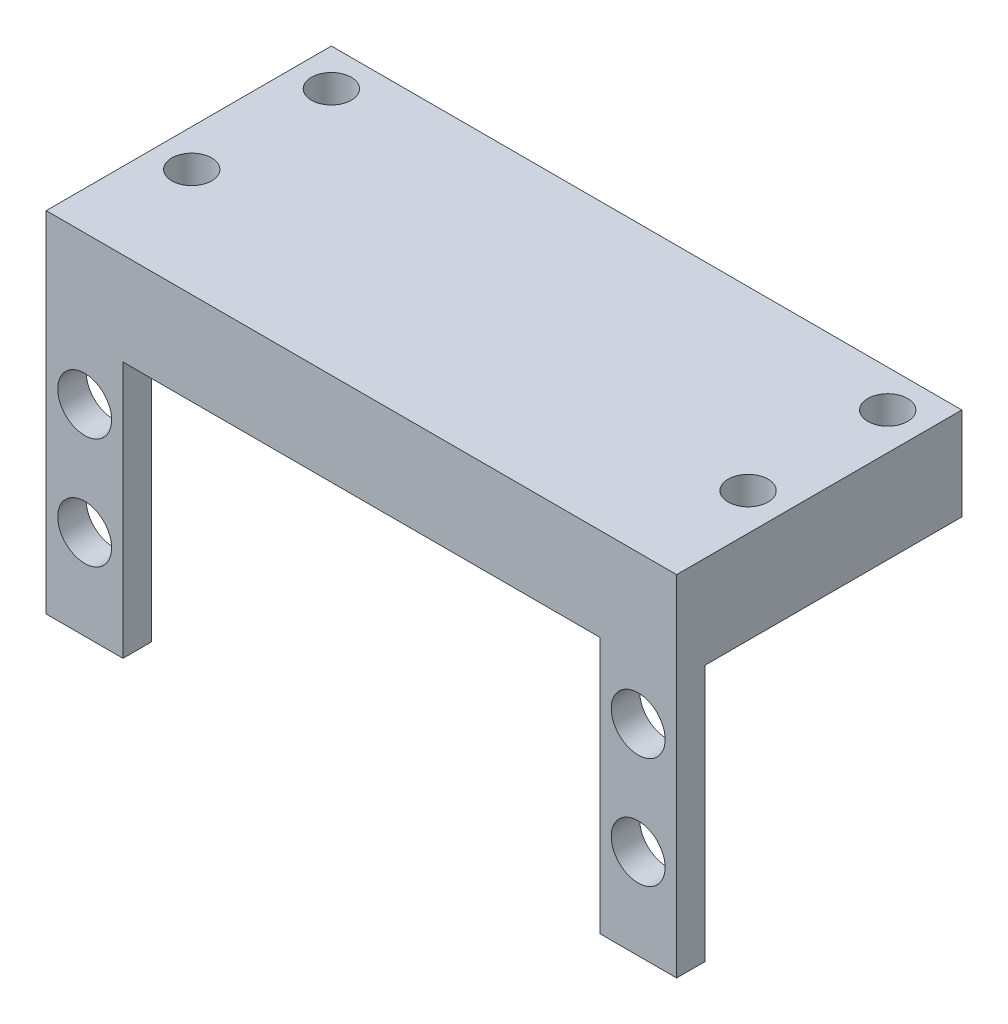
SolidWorks part; units mm, degrees
ref_plane "Front Plane" through (0, 0, 0) normal (0, 0, 1) x (1, 0, 0)
ref_plane "Top Plane" through (0, 0, 0) normal (0, 1, 0) x (1, 0, 0)
ref_plane "Right Plane" through (0, 0, 0) normal (1, 0, 0) x (0, 0, -1)
sketch "Sketch1" plane through (0, 0, 0) normal (0, 1, 0) x (1, 0, 0)
  line L1 (0, 0) -> (56.15, 0)
  line L2 (0, 0) -> (0, 25.4)
  line L3 (0, 25.4) -> (56.15, 25.4)
  line L4 (56.15, 0) -> (56.15, 25.4)
  dimension "D1" = 56.15
  dimension "D2" = 25.4
extrude "Boss-Extrude1" add sketch "Sketch1" against normal blind 2.54
sketch "Sketch2" plane through (0, 0, 0) normal (0, 0, 1) x (1, 0, 0)
  line L1 (0, 0) -> (56.15, 0)
  line L2 (0, 0) -> (0, -25.4)
  line L3 (0, -25.4) -> (56.15, -25.4)
  line L4 (56.15, 0) -> (56.15, -25.4)
  dimension "D1" = 25.4
extrude "Boss-Extrude2" add sketch "Sketch2" against normal blind 2.54
sketch "Sketch3" plane through (0, 0, 0) normal (0, 0, 1) x (1, 0, 0)
  circle A0 centre (3.425, -7.515) radius 2.4
  circle A1 centre (3.425, -17.385) radius 2.4
  circle A2 centre (52.725, -7.515) radius 2.4
  circle A3 centre (52.725, -17.385) radius 2.4
  dimension "D1" = 4.8
  dimension "D2" = 4.8
  dimension "D3" = 4.8
  dimension "D4" = 4.8
extrude "Cut-Extrude1" cut sketch "Sketch3" against normal through all
sketch "Sketch4" plane through (0, 0, 0) normal (0, 0, 1) x (1, 0, 0)
  line L0 (5.825, -7.515) -> (56.15, -7.515)
  line L1 (56.15, -25.4) -> (56.15, 0) construction
  line L2 (1.025, -7.515) -> (-49.3, -7.515)
  line L3 (-49.3, -25.4) -> (-49.3, -2.54)
  line L5 (0, -25.4) -> (56.15, -25.4) construction
  line L7 (-49.3, 0) -> (-49.3, -2.54) construction
  line L8 (0, 0) -> (56.15, 0) construction
  line L9 (50.325, -7.515) -> (0, -7.515)
  line L10 (0, -25.4) -> (0, 0) construction
  line L11 (55.125, -7.515) -> (105.45, -7.515)
  line L12 (-49.3, -2.54) -> (0, -2.54) construction
  line L13 (105.45, -25.4) -> (105.45, -2.54)
  line L14 (-49.3, -25.4) -> (105.45, -25.4)
  line L15 (105.45, -2.54) -> (-49.3, -2.54)
  circle A0 centre (3.425, -7.515) radius 2.4 construction
  circle A1 centre (52.725, -7.515) radius 2.4 construction
  dimension "D1" = 2.54
ref_plane "Plane3" through (0, -2.54, 0) normal (0, -1, 0) x (-1, 0, 0)
sketch "Sketch11" plane through (0, 0, 0) normal (0, 1, 0) x (1, 0, 0)
  line L1 (56.15, 0) -> (0, 0)
  line L2 (56.15, 0) -> (56.15, 25.4)
  line L3 (56.15, 25.4) -> (0, 25.4)
  line L4 (0, 0) -> (0, 25.4)
extrude "Boss-Extrude3" add sketch "Sketch11" along normal blind 5.715
sketch "Sketch6" plane through (0, -2.54, 0) normal (0, -1, 0) x (1, 0, 0)
  line L0 (51.078, -22.102) -> (54.626, -22.102) construction
  line L5 (51.078, -20.328) -> (54.626, -20.328)
  line L6 (51.078, -20.328) -> (51.078, -23.876)
  line L7 (51.078, -23.876) -> (54.626, -23.876)
  line L8 (54.626, -20.328) -> (54.626, -23.876)
  line L9 (52.852, -22.102) -> (52.852, -23.876) construction
  line L10 (52.852, -22.102) -> (52.852, -20.328) construction
  line L11 (56.15, -25.4) -> (54.626, -25.4)
  line L12 (52.852, -20.328) -> (52.852, -11.438) construction
  line L13 (52.852, -11.438) -> (52.852, -9.664) construction
  line L14 (56.15, -25.4) -> (56.15, -23.876)
  line L15 (56.15, -23.876) -> (54.626, -23.876)
  line L16 (54.626, -25.4) -> (54.626, -23.876)
  line L17 (28.075, -25.4) -> (28.075, -2.54) construction
  line L18 (56.15, -25.4) -> (0, -25.4) construction
  line L19 (56.15, -2.54) -> (0, -2.54) construction
  circle A0 centre (52.852, -22.102) radius 1.774
  circle A2 centre (52.852, -9.664) radius 1.774
  circle A3 centre (3.298, -22.102) radius 1.774
  circle A4 centre (3.298, -9.664) radius 1.774
  dimension "D1" = 8.89
  dimension "D3" = 3.548
  dimension "D4" = 3.548
  dimension "D5" = 1.524
  dimension "D6" = 1.524
extrude "Cut-Extrude3" cut sketch "Sketch6" against normal through all contours A0 | A2 | A4 | A3
sketch "Sketch7" plane through (0, 0, 0) normal (0, 0, 1) x (1, 0, 0)
  line L5 (5.825, -7.515) -> (6.841, -7.515)
  line L6 (5.825, -7.515) -> (56.15, -7.515) construction
  line L7 (6.841, -7.515) -> (6.841, -25.4) construction
  line L8 (-49.3, -25.4) -> (105.45, -25.4) construction
  line L9 (50.325, -17.385) -> (49.309, -17.385) construction
  line L12 (105.45, -2.54) -> (-49.3, -2.54) construction
  line L13 (49.309, -17.385) -> (49.309, -25.4) construction
  line L16 (6.841, -2.54) -> (49.309, -2.54)
  line L17 (6.841, -2.54) -> (6.841, -25.4)
  line L18 (6.841, -25.4) -> (49.309, -25.4)
  line L19 (49.309, -2.54) -> (49.309, -25.4)
  circle A0 centre (52.725, -17.385) radius 2.4 construction
  line M8 (0, -25.4) -> (56.15, -25.4)
  dimension "D1" = 1.016
  dimension "D3" = 1.016
extrude "Cut-Extrude4" cut sketch "Sketch7" against normal through all contours L19 L16 L17 M8
sketch "Sketch8" plane through (0, -2.54, 0) normal (0, -1, 0) x (1, 0, 0)
  line L0 (56.15, -25.4) -> (0, -25.4) construction
  line L1 (28.075, -25.4) -> (28.075, 0) construction
